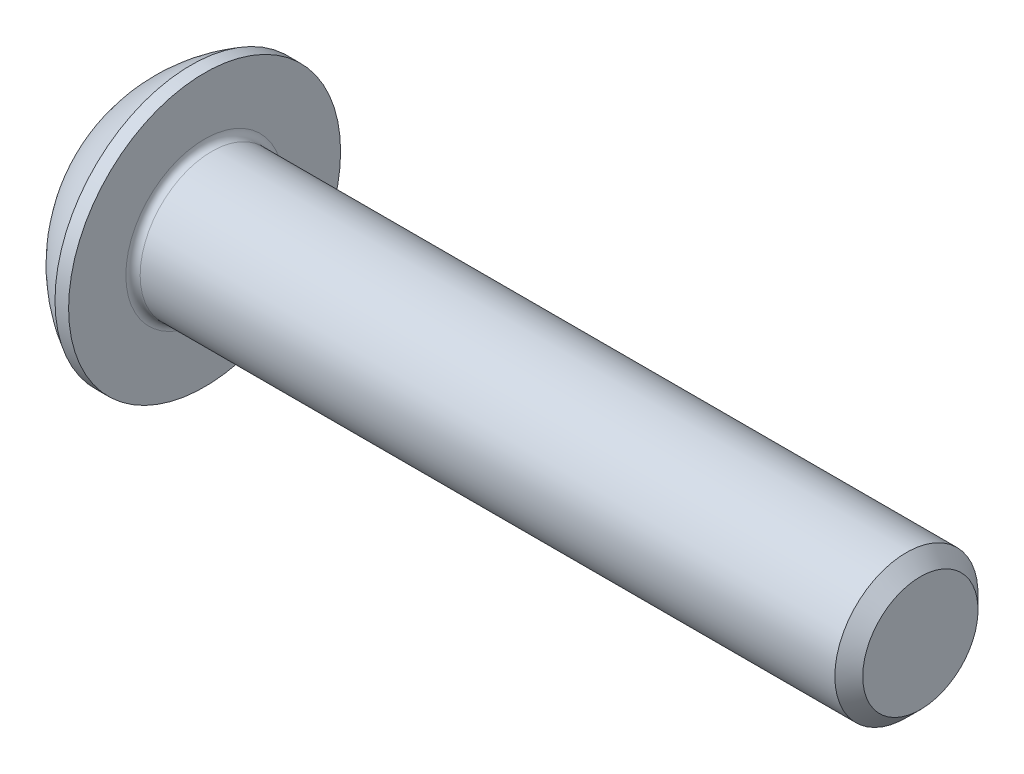
SolidWorks part; units mm, degrees
ref_plane "Plane1" through (0, 0, 0) normal (0, 0, 1) x (1, 0, 0)
ref_plane "Plane2" through (0, 0, 0) normal (0, 1, 0) x (1, 0, 0)
ref_plane "Plane3" through (0, 0, 0) normal (1, 0, 0) x (0, 0, -1)
sketch "BodySke" plane through (0, 0, 0) normal (0, 0, 1) x (1, 0, 0)
  line L0 (22.2, 0) -> (22.2, 1.61)
  line L1 (21.81, 2) -> (2.2, 2)
  line L2 (2.2, 2) -> (2.2, 3.8)
  line L3 (2.2, 3.8) -> (1.82, 3.8)
  line L4 (0, 0) -> (101.6, 0) construction
  line L5 (2.2, -3.8) -> (1.82, -3.8) construction
  line L6 (55.6768, -2) -> (2.2, -2) construction
  line L7 (22.2, 0) -> (0, 0)
  line L8 (0, 1.9) -> (0, -1.9) construction
  line L9 (0, 0) -> (0, 1.9)
  line L10 (22.2, 1.61) -> (21.81, 2)
  line L11 (22.2, -1.61) -> (21.81, -2) construction
  line L12 (2.9, 9.525) -> (2.9, -2) construction
  line L13 (2.2, 9.525) -> (2.2, -2) construction
  arc A1 (0, 1.9) -> (1.82, 3.8) centre (3.8853, 0) cw
  dimension "D1" = 3.8
  dimension "Diameter" = 4
  dimension "Length" = 20
  dimension "Head_dia" = 7.6
  dimension "Head_ht" = 2.2
  dimension "Head_side_ht" = 0.38
  dimension "Minor_dia" = 3.22
  dimension "Body_ch_ang" = 45
  dimension "Advance" = 0.7
  dimension "Thread_nom" = 20
revolve "BaseBody" add sketch "BodySke" angle 360 about L4
cosmetic thread "ThreadCosmetic" [suppressed] parameters "Thread_length"=18.6, "Thread_minor"=3.22
fillet "Fillet1" radius 0.2 1 edges at (2.2, 0, 2)
sketch "Sketch2" plane through (0, 0, 0) normal (0, 0, 1) x (1, 0, 0)
  line L0 (0, 1.25) -> (1.3, 1.25)
  line L1 (1.3, 1.25) -> (2.0217, 0)
  line L3 (2.0217, 0) -> (0, 0)
  line L4 (0, 0) -> (0, 1.25)
  line L5 (0, -1.25) -> (1.3, -1.25) construction
  line L6 (0, 0) -> (47.625, 0) construction
  dimension "D2" = 60
  dimension "PreBroach_depth" = 1.3
  dimension "PreBroach_dia" = 2.5
revolve "PreBroach" cut sketch "Sketch2" angle 360 about L6
sketch "Sketch3" plane through (0, 0, 0) normal (1, 0, 0) x (0, 0, -1)
  line L0 (-1.25, -0.7217) -> (-1.25, 0.7217)
  line L1 (-1.25, 0.7217) -> (0, 1.4434)
  line L2 (0, 1.4434) -> (1.25, 0.7217)
  line L3 (1.25, 0.7217) -> (1.25, -0.7217)
  line L4 (1.25, -0.7217) -> (0, -1.4434)
  line L5 (0, -1.4434) -> (-1.25, -0.7217)
  dimension "D1" = 1.25
  dimension "D2" = 1.25
  dimension "D3" = 2.5
  dimension "Hex_size" = 2.5
extrude "Hex" cut sketch "Sketch3" along normal blind 1.3
sketch "ThdSchSke" plane through (0, 0, 0) normal (0, 0, 1) x (1, 0, 0)
  line L0 (3.6, -1.61) -> (3.3269, -2)
  line L1 (3.6, -1.61) -> (3.8731, -2)
  line L2 (3.8731, -2) -> (3.8731, -2.5)
  line L3 (-3.175, 0) -> (5.1513, 0) construction
  line L5 (3.8731, -2.5) -> (3.3269, -2.5)
  line L6 (3.3269, -2.5) -> (3.3269, -2)
  dimension "Thread_minor" = 3.22
  dimension "Diameter" = 4
  dimension "Start" = 3.6
  dimension "SideAngle" = 55
  dimension "VeeAngle" = 70
  dimension "Overcut" = 5
revolve "ThreadSchematic" [suppressed] cut sketch "ThdSchSke" angle 360 about L3
pattern_linear "ThdSchPat" [suppressed]
equation "\"D1@BodySke\" = \"Head_dia@BodySke\" * .5"
equation "\"Thread_minor@ThreadCosmetic\" = \"Minor_dia@BodySke\""
equation "\"D1@Sketch3\" = \"Hex_size@Sketch3\" / 2"
equation "\"D2@Sketch3\" = \"D1@Sketch3\""
equation "\"D3@Sketch3\" = \"Hex_size@Sketch3\""
equation "\"Thread_length@ThreadCosmetic\" = ((sgn( (\"Length@BodySke\" - \"Advance@BodySke\" * 2.0) - \"Thread_nom@BodySke\" )-1)*( (\"Length@BodySke\" - \"Advance@BodySke\" * 2.0) - \"Thread_nom@BodySke\" ))/-2+ \"Thread_nom@BodySke\""
equation "\"Thread_minor@ThdSchSke\" = \"Minor_dia@BodySke\""
equation "\"Diameter@ThdSchSke\" = \"Diameter@BodySke\""
equation "\"Overcut@ThdSchSke\" = \"Diameter@BodySke\" * 1.25"
equation "\"Start@ThdSchSke\" = \"Head_ht@BodySke\" + \"Length@BodySke\" - \"Thread_length@ThreadCosmetic\"  '---Non-countersunk---"
equation "\"Num_threads@ThdSchPat\" = int( \"Thread_length@ThreadCosmetic\" / \"Advance@BodySke\" + 0.999 )  + 1"
equation "\"Advance@ThdSchPat\" = \"Thread_length@ThreadCosmetic\" /  (\"Num_threads@ThdSchPat\" - 1) 'relax it"
equation "\"Num_threads@ThdSchPat\" = \"Num_threads@ThdSchPat\" - sgn( \"Num_threads@ThdSchPat\" - 1) '---chamfered tips only---"
